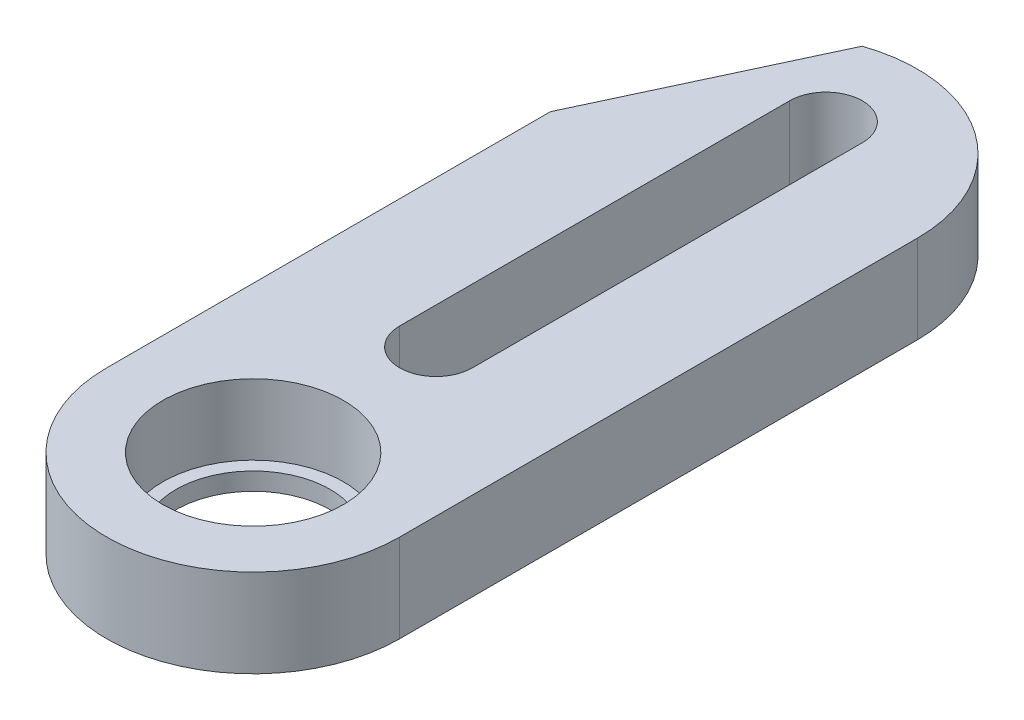
SolidWorks part; units mm, degrees
ref_plane "Front Plane" through (0, 0, 0) normal (0, 0, 1) x (1, 0, 0)
ref_plane "Top Plane" through (0, 0, 0) normal (0, 1, 0) x (1, 0, 0)
ref_plane "Right Plane" through (0, 0, 0) normal (1, 0, 0) x (0, 0, -1)
sketch "Sketch1" plane through (0, 0, 0) normal (0, 1, 0) x (1, 0, 0)
  line L0 (-6.65, 0) -> (-6.65, 23.5)
  line L1 (6.65, 23.5) -> (6.65, 0)
  line L2 (0, 26) -> (0, 8.3) construction
  line L3 (1.65, 26) -> (1.65, 8.3)
  line L4 (-1.65, 26) -> (-1.65, 8.3)
  line L5 (0, 27.65) -> (0, 30.15) construction
  line L7 (0, 6.65) -> (0, 4.1) construction
  circle A0 centre (0, 0) radius 4.1
  circle A1 centre (0, 0) radius 6.65
  arc A2 (-6.65, 23.5) -> (6.65, 23.5) centre (0, 23.5) cw
  arc A3 (1.65, 26) -> (-1.65, 26) centre (0, 26) ccw
  arc A4 (-1.65, 8.3) -> (1.65, 8.3) centre (0, 8.3) ccw
  point P8 (0, 17.15)
  point P16 (0, 6.65)
  point P20 (0, 0)
  point P21 (0, 0)
  point P23 (0, 18.55)
  point P24 (0, 18.55)
  point P25 (0, 0)
  dimension "D1" = 8.2
  dimension "D2" = 3.3
  dimension "D3" = 5
  dimension "D4" = 21
  dimension "D5" = 2.5
extrude "Boss-Extrude1" add sketch "Sketch1" along normal blind 4 contours A2 L0 A1 L1 A4 L4 A3 L3 | A1 A0
sketch "Sketch2" plane through (0, 0, 0) normal (0, 1, 0) x (1, 0, 0)
  circle A0 centre (0, 0) radius 4.1
  circle A1 centre (0, 0) radius 4.1 construction
extrude "Boss-Extrude2" add sketch "Sketch2" along normal blind 0.8
sketch "Sketch3" plane through (0, 0.8, 0) normal (0, 1, 0) x (1, 0, 0)
  circle A0 centre (0, 0) radius 3.5
  dimension "D1" = 7
extrude "Cut-Extrude1" cut sketch "Sketch3" against normal through all
sketch "Sketch4" plane through (0, 0, 0) normal (0, -1, 0) x (1, 0, 0)
  line L0 (-2.15, -29.7929) -> (-2.15, -12.7276) construction
  line L1 (-6.65, -20.1426) -> (-2.15, -29.7929)
  line L2 (-6.65, 0) -> (-6.65, -23.5) construction
  line L4 (-6.65, -20.1426) -> (-6.65, -23.5)
  line L5 (-1.65, -26) -> (-1.65, -8.3) construction
  arc A0 (-6.65, -23.5) -> (6.65, -23.5) centre (0, -23.5) ccw construction
  arc A1 (-6.65, -23.5) -> (-2.15, -29.7929) centre (0, -23.5) ccw
  dimension "D1" = 25
  dimension "D2" = 0.5
extrude "Cut-Extrude2" cut sketch "Sketch4" against normal through all
